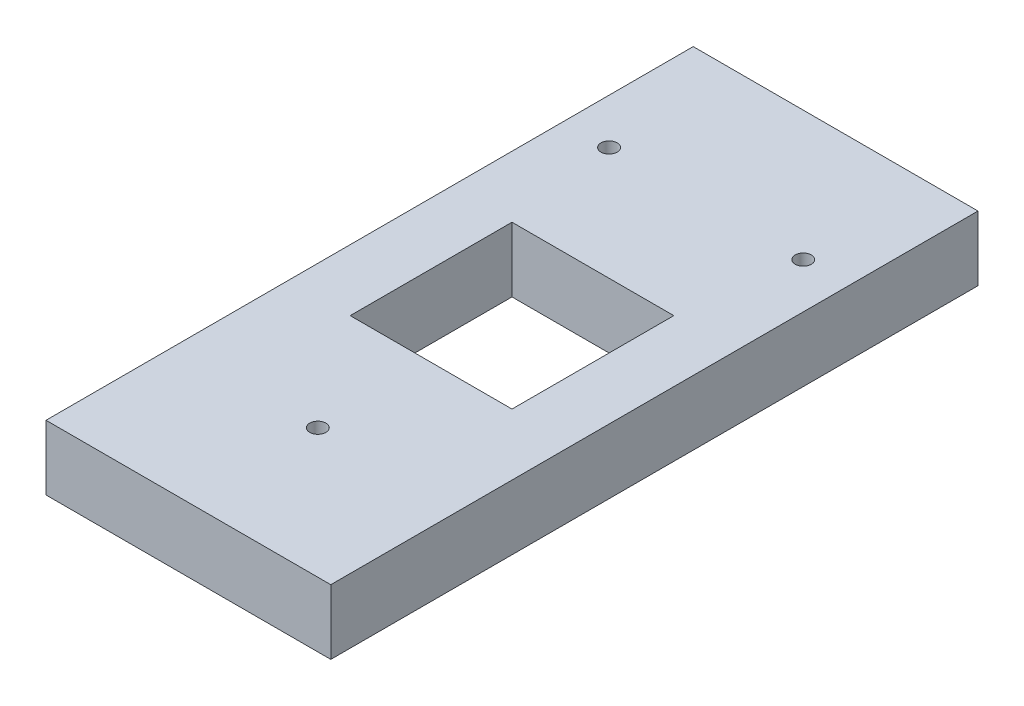
SolidWorks part; units mm, degrees
material "6061 Alloy"
ref_plane "Front Plane" through (0, 0, 0) normal (0, 0, 1) x (1, 0, 0)
ref_plane "Top Plane" through (0, 0, 0) normal (0, 1, 0) x (1, 0, 0)
ref_plane "Right Plane" through (0, 0, 0) normal (1, 0, 0) x (0, 0, -1)
sketch "Sketch1" plane through (0, 0, 0) normal (0, 1, 0) x (1, 0, 0)
  line L1 (-55.88, 127) -> (55.88, 127)
  line L2 (-55.88, 127) -> (-55.88, -127)
  line L3 (-55.88, -127) -> (55.88, -127)
  line L4 (55.88, 127) -> (55.88, -127)
  dimension "D1" = 55.88
  dimension "D2" = 55.88
  dimension "D3" = 127
  dimension "D4" = 127
extrude "Boss-Extrude1" add sketch "Sketch1" along normal mid plane 25.4
sketch "Sketch2" plane through (0, 12.7, 0) normal (0, 1, 0) x (1, 0, 0)
  line L1 (-31.75, 31.75) -> (31.75, 31.75)
  line L2 (-31.75, 31.75) -> (-31.75, -31.75)
  line L3 (-31.75, -31.75) -> (31.75, -31.75)
  line L4 (31.75, 31.75) -> (31.75, -31.75)
  dimension "D1" = 31.75
  dimension "D2" = 31.75
  dimension "D3" = 31.75
  dimension "D4" = 31.75
extrude "Cut-Extrude1" cut sketch "Sketch2" against normal blind 25.4
sketch "Sketch3" plane through (0, 12.7, 0) normal (0, 1, 0) x (1, 0, 0)
  circle A0 centre (0, -76.2) radius 3.175
  circle A1 centre (38.1, 76.2) radius 3.175
  circle A2 centre (-38.1, 76.2) radius 3.175
  dimension "D1" = 6.35
  dimension "D2" = 6.35
  dimension "D3" = 6.35
  dimension "D4" = 38.1
  dimension "D5" = 38.1
  dimension "D6" = 76.2
  dimension "D7" = 76.2
extrude "Cut-Extrude2" cut sketch "Sketch3" against normal up to next
